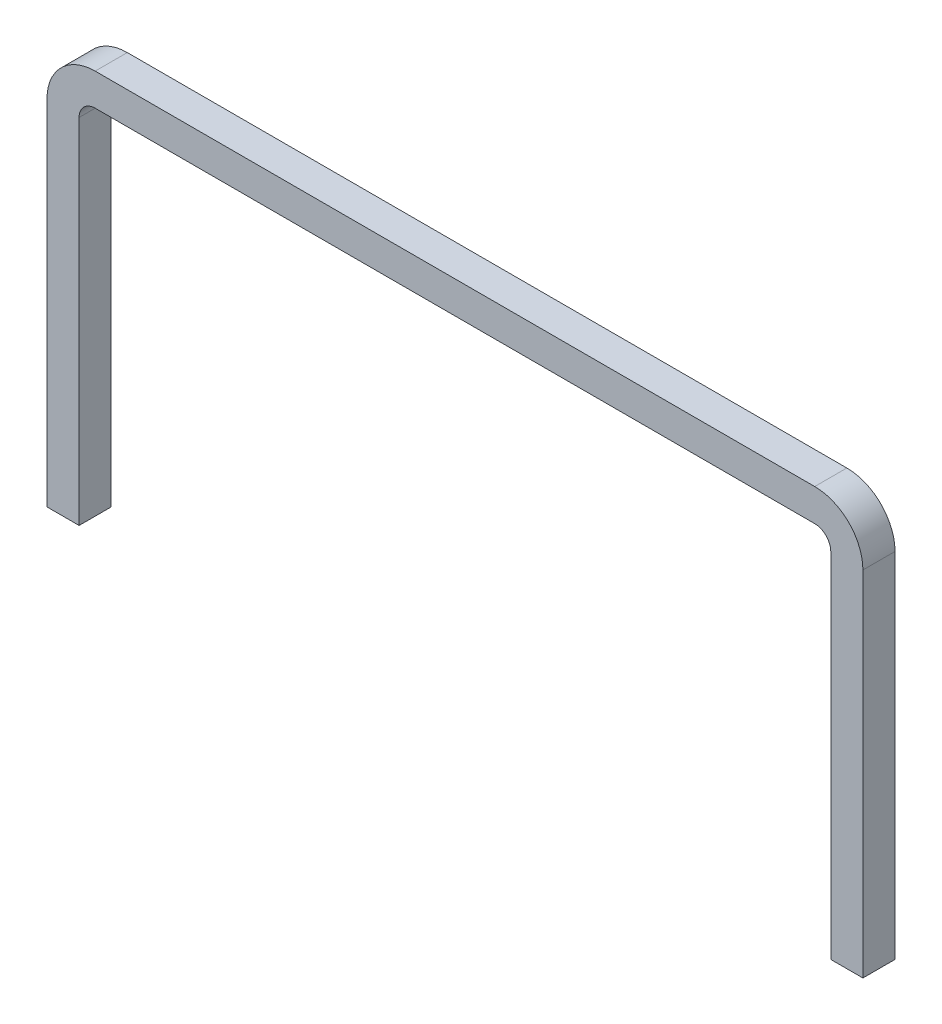
SolidWorks part; units mm, degrees
ref_plane "Front Plane" through (0, 0, 0) normal (0, 0, 1) x (1, 0, 0)
ref_plane "Top Plane" through (0, 0, 0) normal (0, 1, 0) x (1, 0, 0)
ref_plane "Right Plane" through (0, 0, 0) normal (1, 0, 0) x (0, 0, -1)
sketch "Sketch1" plane through (0, 0, 0) normal (0, 0, 1) x (1, 0, 0)
  line L0 (0, 0) -> (0, 33.9091) construction
  line L1 (-5.6, 0.5) -> (5.6, 0.5)
  line L2 (-6.1, 0) -> (-6.1, -5.5)
  line L4 (6.1, 0) -> (6.1, -5.5)
  line L5 (0, 0) -> (57.8715, 0) construction
  arc A0 (-5.6, 0.5) -> (-6.1, 0) centre (-5.6, 0) ccw
  arc A1 (6.1, 0) -> (5.6, 0.5) centre (5.6, 0) ccw
  point P7 (0, 0.5)
  point P11 (-6.1, 0.5)
  point P14 (6.1, 0.5)
  dimension "D3" = 0.5
  dimension "D1" = 12.2
  dimension "D2" = 6
extrude "Extrude-Thin2" add sketch "Sketch1" along normal mid plane 0.5 thin thin type mid plane wall 0.5
